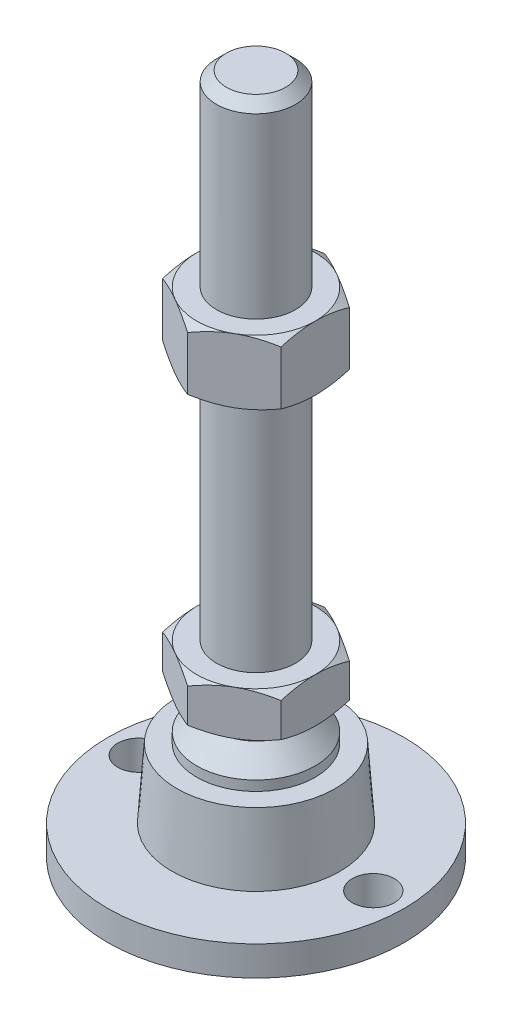
SolidWorks part; units mm, degrees
ref_plane "Спереди" through (0, 0, 0) normal (0, 0, 1) x (1, 0, 0)
ref_plane "Сверху" through (0, 0, 0) normal (0, 1, 0) x (1, 0, 0)
ref_plane "Справа" through (0, 0, 0) normal (1, 0, 0) x (0, 0, -1)
sketch "Эскиз1" plane through (0, 0, 0) normal (0, 0, 1) x (1, 0, 0)
  line L0 (0, 0) -> (-30, 0)
  line L3 (-30, 0) -> (-30, 6)
  line L12 (-8, 38) -> (-8, 136)
  line L13 (-8, 136) -> (-6, 138)
  line L14 (-6, 138) -> (0, 138)
  line L15 (0, 138) -> (0, 0) construction
  line L16 (-30, 6) -> (-17, 6)
  line L17 (0, 0) -> (0, 138)
  line L18 (0, 0) -> (0, -7.9595) construction
  line L19 (-8, 38) -> (-8, 29)
  line L21 (-12, 20) -> (-16, 20)
  line L22 (-17, 6) -> (-16, 20)
  line L23 (-12, 20) -> (-12, 22)
  line L24 (-12, 22) -> (-8, 26)
  line L25 (-8, 26) -> (-8, 29)
  line L26 (-8, 38) -> (0, 38) construction
  point P8 (-8, 87)
revolve "Повернуть1" add sketch "Эскиз1" angle 360 about L17
ref_plane "Плоскость2" through (0, 29, 0) normal (0, 1, 0) x (1, 0, 0)
sketch "Эскиз2" plane through (0, 29, 0) normal (0, 1, 0) x (1, 0, 0)
  line L1 (0, 13.8564) -> (-12, 6.9282)
  line L2 (-12, 6.9282) -> (-12, -6.9282)
  line L3 (-12, -6.9282) -> (0, -13.8564)
  line L4 (0, -13.8564) -> (12, -6.9282)
  line L5 (12, -6.9282) -> (12, 6.9282)
  line L6 (12, 6.9282) -> (0, 13.8564)
  circle A0 centre (0, 0) radius 12 construction
  dimension "D1" = 24
extrude "Бобышка-Вытянуть1" add sketch "Эскиз2" along normal up to vertex (9 mm away) up to point (-8, 38, 0)
ref_plane "Плоскость1" through (0, 87, 0) normal (0, 1, 0) x (1, 0, 0)
sketch "Эскиз3" plane through (0, 87, 0) normal (0, 1, 0) x (1, 0, 0)
  line L6 (12, 6.9282) -> (0, 13.8564)
  line L7 (0, 13.8564) -> (-12, 6.9282)
  line L8 (-12, 6.9282) -> (-12, -6.9282)
  line L9 (-12, -6.9282) -> (0, -13.8564)
  line L10 (0, -13.8564) -> (12, -6.9282)
  line L11 (12, -6.9282) -> (12, 6.9282)
  line L12 (12, 6.9282) -> (0, 13.8564)
  line L13 (0, 13.8564) -> (-12, 6.9282)
  line L14 (-12, 6.9282) -> (-12, -6.9282)
  line L15 (-12, -6.9282) -> (0, -13.8564)
  line L16 (0, -13.8564) -> (12, -6.9282)
  line L17 (12, -6.9282) -> (12, 6.9282)
  dimension "D1" = 0
extrude "Бобышка-Вытянуть2" add sketch "Эскиз3" along normal blind 13
sketch "Эскиз4" plane through (0, 0, 0) normal (0, 0, 1) x (1, 0, 0)
  line L0 (-12, 100) -> (-23.2583, 93.5)
  line L1 (-23.2583, 93.5) -> (-23.2583, 100)
  line L2 (-23.2583, 100) -> (-12, 100)
  line L3 (-23.2583, 93.5) -> (-12, 87)
  line L4 (50, 87) -> (-50, 87) construction
  line L5 (-12, 87) -> (-23.2583, 87)
  line L6 (-23.2583, 87) -> (-23.2583, 93.5)
  line L7 (-12, 100) -> (-12, 87) construction
  line L8 (-12, 38) -> (-19.7942, 38)
  line L9 (-19.7942, 38) -> (-19.7942, 33.5)
  line L10 (-19.7942, 33.5) -> (-12, 38)
  line L11 (-12, 29) -> (-19.7942, 33.5)
  line L12 (-19.7942, 33.5) -> (-19.7942, 29)
  line L13 (-19.7942, 29) -> (-12, 29)
  line L14 (0, 138) -> (0, 96.3793) construction
  line L15 (50, 29) -> (-50, 29) construction
  dimension "D1" = 30
  dimension "D2" = 30
revolve "Вырез-Повернуть2" cut sketch "Эскиз4" angle 360 about L14
sketch "Эскиз5" plane through (0, 6, 0) normal (0, 1, 0) x (1, 0, 0)
  line L0 (23.75, 0) -> (-23.75, 0) construction
  circle A0 centre (-23.75, 0) radius 4.25
  circle A1 centre (23.75, 0) radius 4.25
  circle A2 centre (0, 0) radius 30 construction
  dimension "D1" = 8.5
  dimension "D2" = 2
extrude "Вырез-Вытянуть1" cut sketch "Эскиз5" against normal through all
equation "\"D13@Эскиз1\"=\"D12@Эскиз1\"/2"
